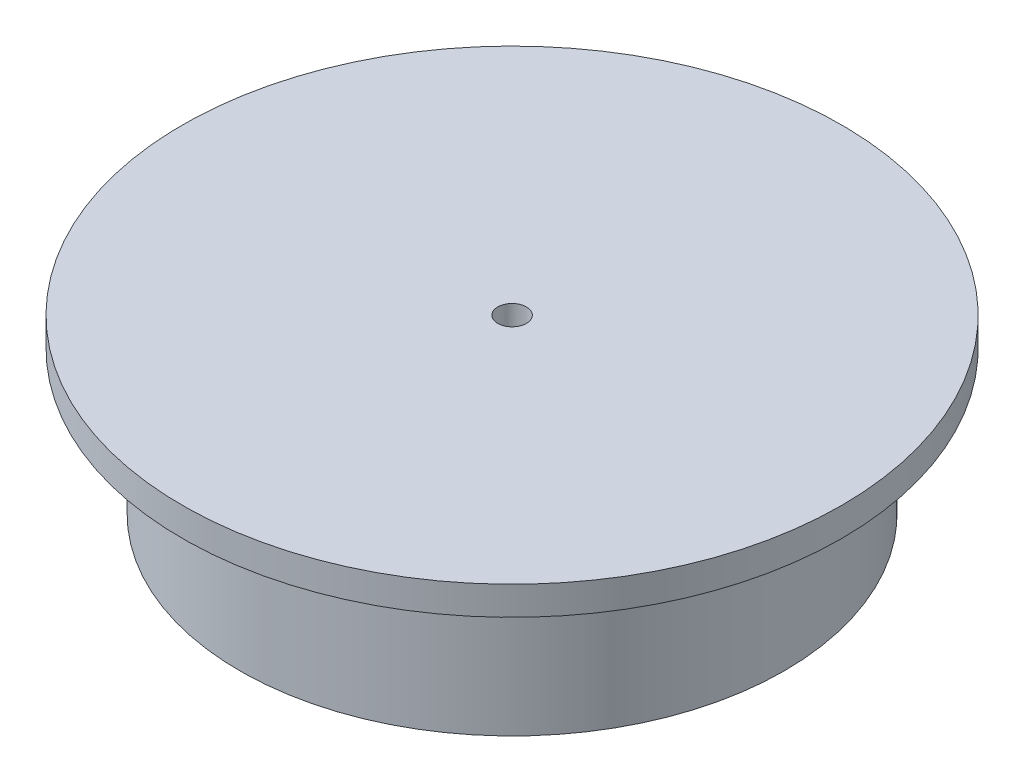
SolidWorks part; units mm, degrees
ref_plane "Front Plane" through (0, 0, 0) normal (0, 0, 1) x (1, 0, 0)
ref_plane "Top Plane" through (0, 0, 0) normal (0, 1, 0) x (1, 0, 0)
ref_plane "Right Plane" through (0, 0, 0) normal (1, 0, 0) x (0, 0, -1)
sketch "Sketch1" plane through (0, 0, 0) normal (0, 0, 1) x (1, 0, 0)
  line L24 (0, 10) -> (-2.5, 10)
  line L25 (-2.5, 10) -> (-12.6821, 20.1821)
  line L26 (-12.6821, 20.1821) -> (-22.5, 10.3641)
  line L27 (-22.5, 10.3641) -> (-32.6239, 20.488)
  line L28 (-32.6239, 20.488) -> (-42.5, 10.6119)
  line L29 (-42.5, 10.6119) -> (-47.5, 10.6119)
  line L30 (-47.5, 10.6119) -> (-47.5, 35.6119)
  line L31 (0, 10) -> (0, 40.6119)
  line L32 (0, 40.6119) -> (-57.5, 40.6119)
  line L33 (-57.5, 40.6119) -> (-57.5, 35.6119)
  line L34 (-57.5, 35.6119) -> (-47.5, 35.6119)
  line L35 (0, 40.6119) -> (0, 66.0983)
  dimension "D1" = 25
  dimension "D2" = 2.5
  dimension "D3" = 135
  dimension "D4" = 20
  dimension "D5" = 20
  dimension "D6" = 5
  dimension "D7" = 10
  dimension "D8" = 5
revolve "Revolve1" add sketch "Sketch1" angle 360 about L35
sketch "Sketch2" plane through (0, 10, 0) normal (0, -1, 0) x (1, 0, 0)
  circle A0 centre (0, 0) radius 2.5
extrude "Cut-Extrude1" cut sketch "Sketch2" against normal blind 40
